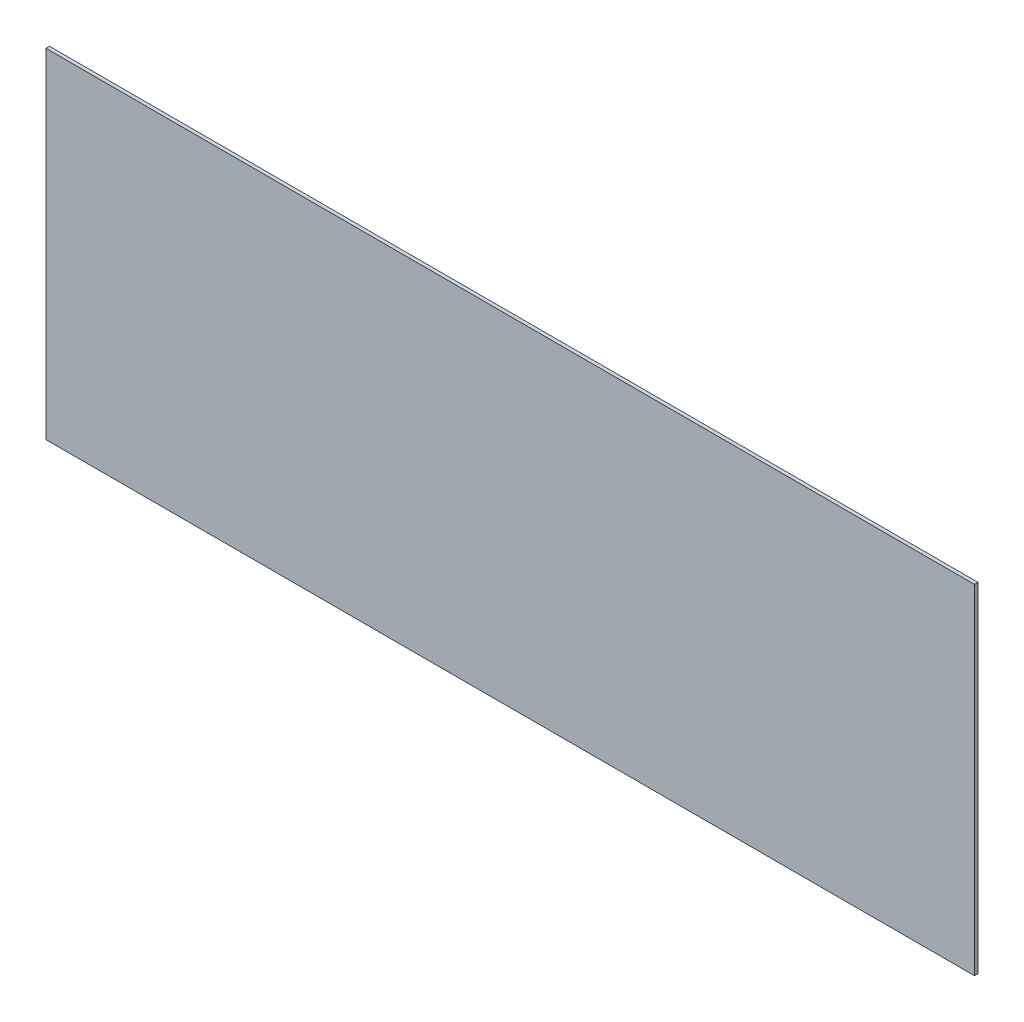
SolidWorks part; units mm, degrees
ref_plane "Front Plane" through (0, 0, 0) normal (0, 0, 1) x (1, 0, 0)
ref_plane "Top Plane" through (0, 0, 0) normal (0, 1, 0) x (1, 0, 0)
ref_plane "Right Plane" through (0, 0, 0) normal (1, 0, 0) x (0, 0, -1)
sketch "Sketch1" plane through (0, 0, 0) normal (0, 0, 1) x (1, 0, 0)
  line L1 (417.5125, -152.4) -> (-417.5125, -152.4)
  line L2 (417.5125, -152.4) -> (417.5125, 152.4)
  line L3 (417.5125, 152.4) -> (-417.5125, 152.4)
  line L4 (-417.5125, -152.4) -> (-417.5125, 152.4)
  line L5 (417.5125, -152.4) -> (-417.5125, 152.4) construction
  line L6 (417.5125, 152.4) -> (-417.5125, -152.4) construction
  point P0 (0, 0)
  dimension "D1" = 835.025
  dimension "D2" = 304.8
extrude "Boss-Extrude1" add sketch "Sketch1" along normal mid plane 3.175
